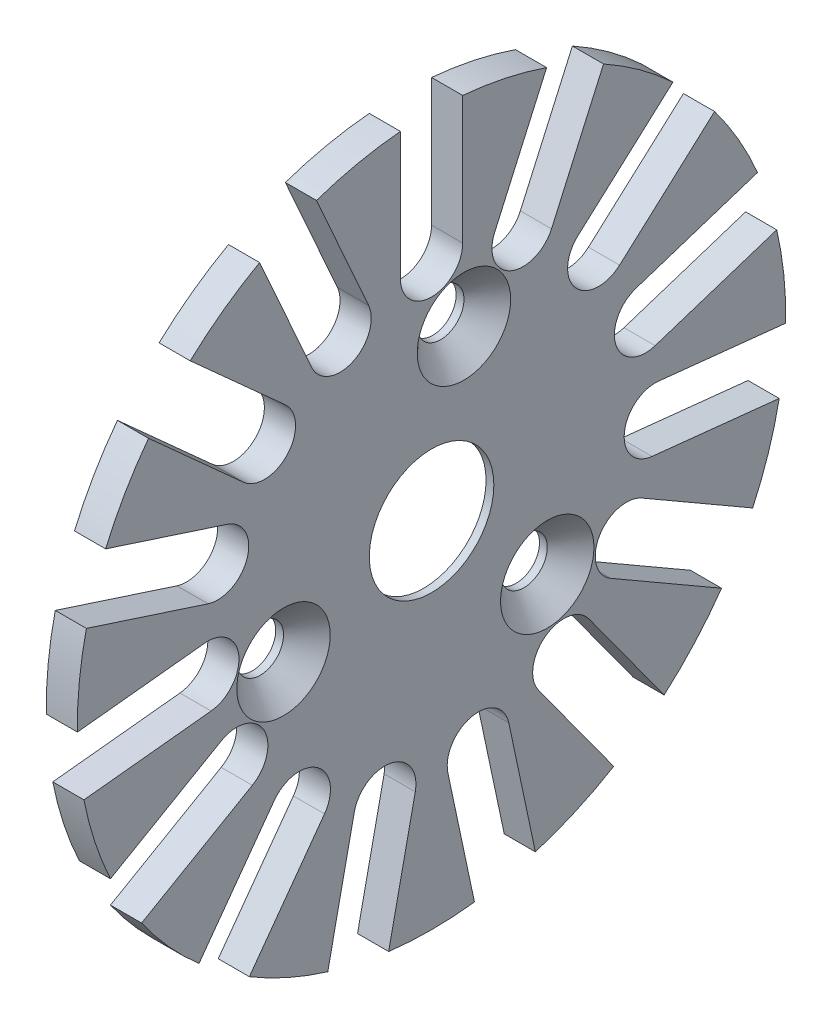
SolidWorks part; units mm, degrees
ref_plane "Front Plane" through (0, 0, 0) normal (0, 0, 1) x (1, 0, 0)
ref_plane "Top Plane" through (0, 0, 0) normal (0, 1, 0) x (1, 0, 0)
ref_plane "Right Plane" through (0, 0, 0) normal (1, 0, 0) x (0, 0, -1)
sketch "Sketch1" plane through (0, 0, 0) normal (1, 0, 0) x (0, 0, -1)
  circle A0 centre (0, 0) radius 22.75
  dimension "D1" = 45.5
extrude "Boss-Extrude1" add sketch "Sketch1" along normal blind 2
sketch "Sketch3" plane through (2, 0, 0) normal (1, 0, 0) x (0, 0, -1)
  circle A0 centre (0, 0) radius 4
  dimension "D1" = 8
extrude "Cut-Extrude2" cut sketch "Sketch3" against normal up to next
sketch "Sketch2" plane through (2, 0, 0) normal (1, 0, 0) x (0, 0, -1)
  line L0 (2.0791, 9.7815) -> (0, 0) construction
  line L1 (0, 0) -> (4, 0) construction
  circle A0 centre (2.0791, 9.7815) radius 1.5
  circle A1 centre (0, 0) radius 4 construction
  dimension "D1" = 3
  dimension "D2" = 10
  dimension "D3" = 78
extrude "Cut-Extrude1" cut sketch "Sketch2" against normal up to next (2 mm away)
chamfer "Chamfer1" distance 1.5 angle 45 1 edges at (2, 9.7815, -3.5791)
pattern_circular "CirPattern1" count 3 over 360 about axis through (0, 0, 0) along (1, 0, 0) of "Cut-Extrude1", "Chamfer1"
sketch "Sketch4" plane through (2, 0, 0) normal (1, 0, 0) x (0, 0, -1)
  line L0 (-2, 22.75) -> (-2, 14.45)
  line L1 (2, 14.45) -> (2, 22.75)
  line L2 (2, 22.75) -> (-2, 22.75)
  arc A0 (-2, 14.45) -> (2, 14.45) centre (0, 14.45) ccw
  circle A1 centre (0, 0) radius 22.75 construction
  dimension "D1" = 4
  dimension "D2" = 8.3
extrude "Cut-Extrude3" cut sketch "Sketch4" against normal up to next (2 mm away)
pattern_circular "CirPattern2" count 15 over 360 about axis through (0, 0, 0) along (1, 0, 0) of "Cut-Extrude3"
sketch "Sketch5" plane through (0, 0, 0) normal (-1, 0, 0) x (0, 0, 1)
  circle A0 centre (0, 0) radius 7
  dimension "D1" = 14
extrude "Cut-Extrude4" cut sketch "Sketch5" against normal blind 1.5
